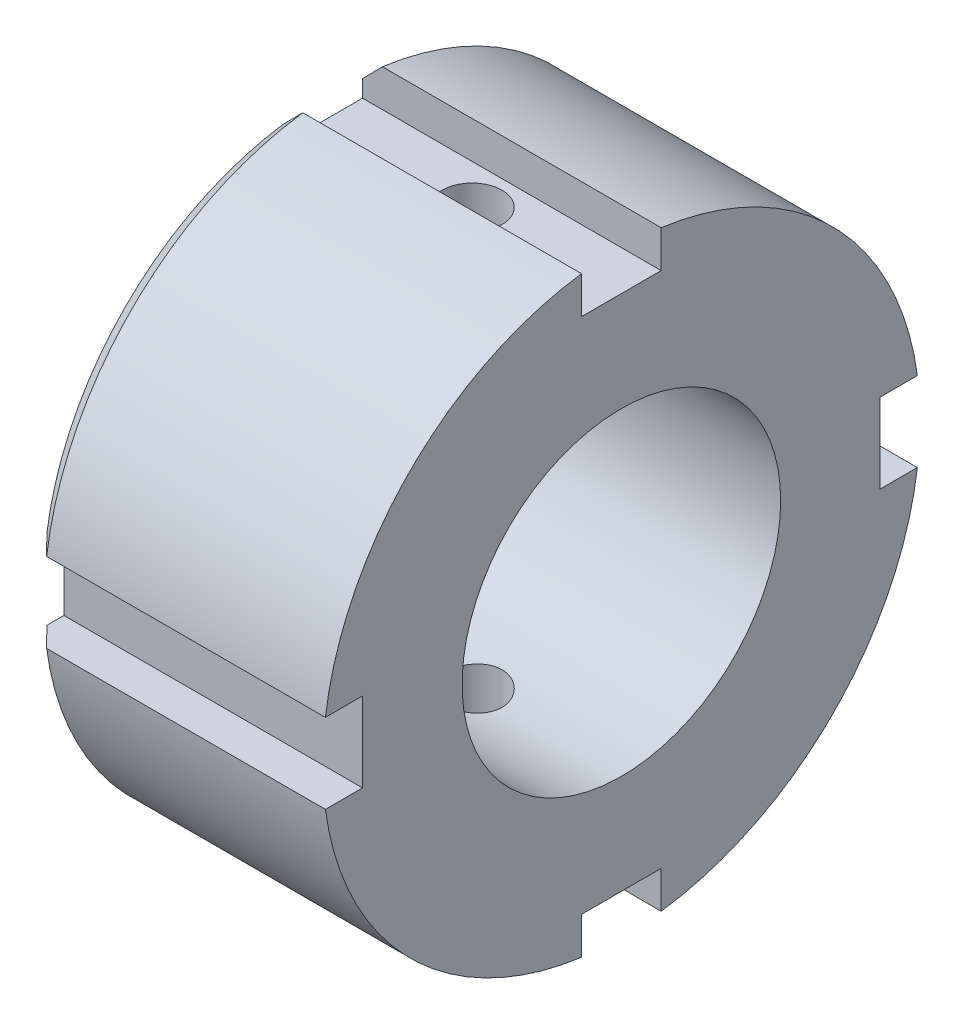
SolidWorks part; units mm, degrees
ref_plane "Front Plane" through (0, 0, 0) normal (0, 0, 1) x (1, 0, 0)
ref_plane "Top Plane" through (0, 0, 0) normal (0, 1, 0) x (1, 0, 0)
ref_plane "Right Plane" through (0, 0, 0) normal (1, 0, 0) x (0, 0, -1)
sketch "Sketch1" plane through (0, 0, 0) normal (1, 0, 0) x (0, 0, -1)
  circle A0 centre (0, 0) radius 15
  dimension "D1" = 30
extrude "Boss-Extrude1" add sketch "Sketch1" along normal blind 15
sketch "Sketch2" plane through (15, 0, 0) normal (1, 0, 0) x (0, 0, -1)
  circle A0 centre (0, 0) radius 8
  dimension "D1" = 16
extrude "Cut-Extrude1" cut sketch "Sketch2" against normal through all
chamfer "Chamfer1" distance 1 angle 45 1 edges at (0, 0, -15)
sketch "Sketch3" plane through (15, 0, 0) normal (1, 0, 0) x (0, 0, -1)
  line L0 (0, 0) -> (0, 15) construction
  line L2 (-2, 17) -> (2, 17)
  line L3 (-2, 17) -> (-2, 13)
  line L4 (-2, 13) -> (2, 13)
  line L5 (2, 17) -> (2, 13)
  line L6 (-2, 17) -> (2, 13) construction
  line L7 (-2, 13) -> (2, 17) construction
  circle A0 centre (0, 0) radius 15 construction
  dimension "D1" = 4
  dimension "D2" = 4
extrude "Cut-Extrude2" cut sketch "Sketch3" against normal through all
pattern_circular "CirPattern1" count 4 over 360 about axis through (0, 0, 0) along (1, 0, 0) of "Cut-Extrude2"
sketch "Sketch4" plane through (0, 0, 0) normal (0, 1, 0) x (1, 0, 0)
  line L0 (0, 0) -> (15, 0) construction
  line L1 (15, -2) -> (15, 2) construction
  circle A0 centre (7.5, 0) radius 1.5
  point P7 (7.5, 0)
  dimension "D1" = 3
extrude "Cut-Extrude4" cut sketch "Sketch4" against normal through all and the other way blind 18
